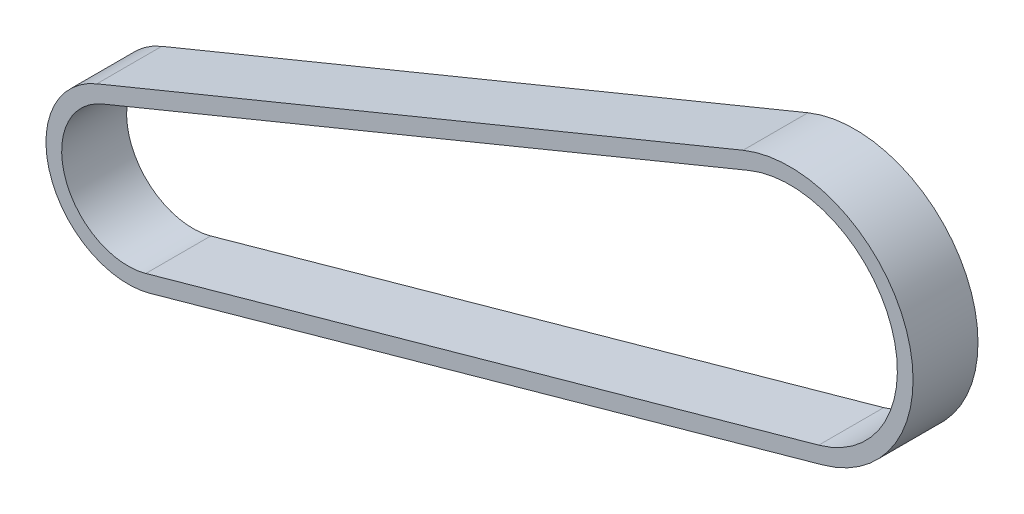
SolidWorks part; units mm, degrees
material "NEOPRENE"
ref_plane "Front Plane" through (0, 0, 0) normal (0, 0, 1) x (1, 0, 0)
ref_plane "Top Plane" through (0, 0, 0) normal (0, 1, 0) x (1, 0, 0)
ref_plane "Right Plane" through (0, 0, 0) normal (1, 0, 0) x (0, 0, -1)
sketch "Sketch2" plane through (0, 0, 0) normal (0, 0, 1) x (1, 0, 0)
  line L0 (0, 0) -> (1, 0) construction
  line L1 (0, 0) -> (0, 1) construction
  line L2 (-63.4792, -15.3491) -> (-3.7756, 9.1871)
  line L3 (2.67, -9.5671) -> (-59.5029, -26.9186)
  arc A0 (-59.5029, -26.9186) -> (-63.4792, -15.3491) centre (-61.15, -21.0166) cw
  arc A1 (-3.7756, 9.1871) -> (2.67, -9.5671) centre (0, 0) cw
ref_plane "Plane2" through (-63.4792, -15.3491, 0) normal (0.9249, 0.3801, 0) x (0, 0, -1)
sketch "Sketch3" plane through (-63.4792, -15.3491, 0) normal (0.9249, 0.3801, 0) x (0, 0, -1)
  line L0 (3, 1.45) -> (3, 0)
  line L1 (3, 1.45) -> (-3, 1.45)
  line L2 (3, 0) -> (-3, 0)
  line L3 (-3, 1.45) -> (-3, 0)
  line L4 (3, 1.45) -> (-3, 0) construction
  line L5 (3, 0) -> (-3, 1.45) construction
  point P0 (0, 0)
  point P1 (0, 0.725)
  dimension "D1" = 1.45
  dimension "D2" = 6
sweep "Sweep1" add profiles "Sketch3" path "Sketch2"
